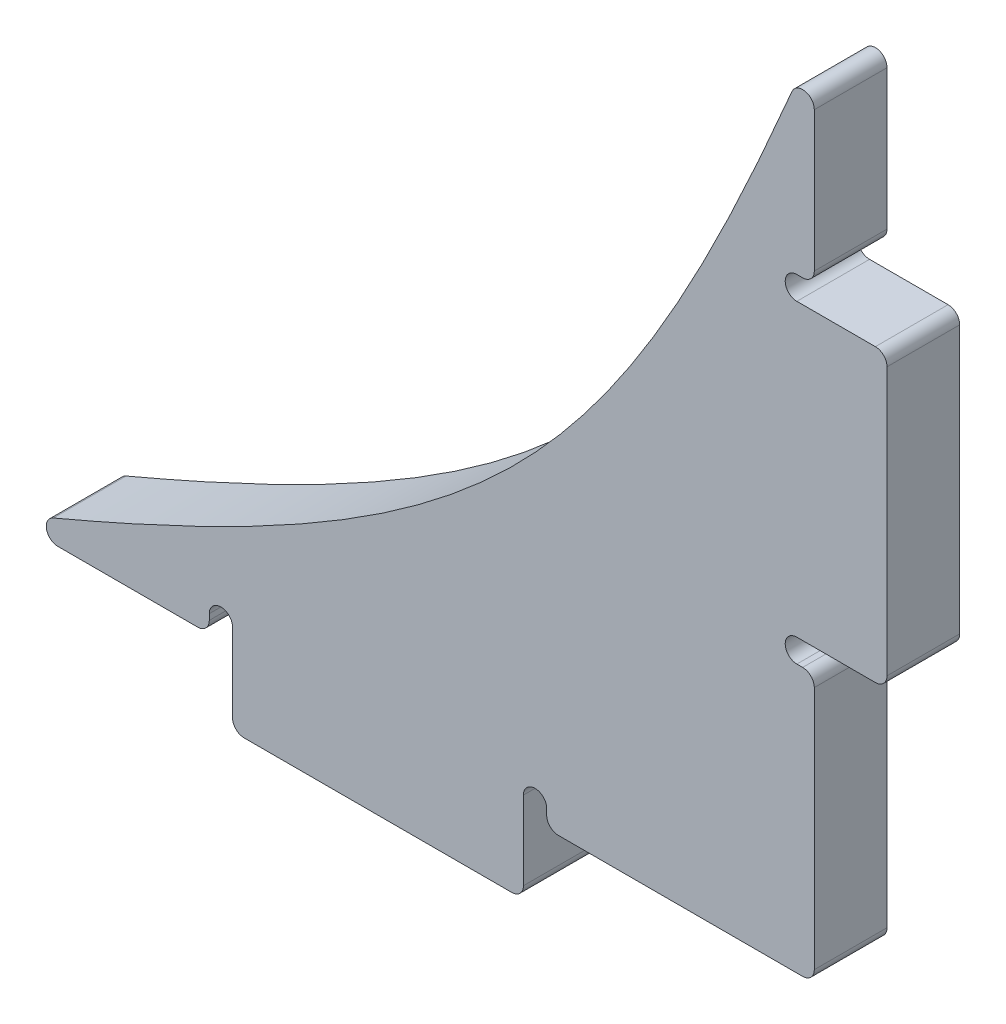
SolidWorks part; units mm, degrees
material "6061-T6 (SS)"
ref_plane "Front Plane" through (0, 0, 0) normal (0, 0, 1) x (1, 0, 0)
ref_plane "Top Plane" through (0, 0, 0) normal (0, 1, 0) x (1, 0, 0)
ref_plane "Right Plane" through (0, 0, 0) normal (1, 0, 0) x (0, 0, -1)
sketch "Sketch1" plane through (0, 0, 0) normal (0, 0, 1) x (1, 0, 0)
  line L0 (22.86, 22.86) -> (14.0603, 1.4879) construction
  line L1 (22.86, -12.7) -> (-12.7, -12.7)
  line L2 (22.86, -12.7) -> (22.86, 22.86)
  line L5 (5.08, 5.08) -> (22.86, -12.7) construction
  line L6 (22.86, 22.86) -> (-12.7, -12.7) construction
  line L7 (14.0603, 1.4879) -> (8.6721, -3.9003) construction
  line L8 (8.6721, -3.9003) -> (-12.7, -12.7) construction
  spline S0 degree 3 poles (22.86, 22.86) (14.0603, 1.4879) (8.6721, -3.9003) (-12.7, -12.7) knots 0 0 0 0 1 1 1 1
  point P0 (0, 0)
  point P9 (11.3662, -1.2062)
  dimension "D1" = 35.56
  dimension "D2" = 35.56
  dimension "D3" = 7.62
  dimension "D4" = 12.7
  dimension "D5" = 17.78
extrude "Boss-Extrude1" add sketch "Sketch1" along normal blind 3.175
sketch "Sketch2" plane through (0, -12.7, 0) normal (0, -1, 0) x (1, 0, 0)
  line L0 (-12.7, 3.175) -> (22.86, 3.175) construction
  line L1 (-2.54, 3.175) -> (10.16, 3.175)
  line L2 (-2.54, 3.175) -> (-2.54, 0)
  line L3 (-2.54, 0) -> (10.16, 0)
  line L4 (10.16, 3.175) -> (10.16, 0)
  line L5 (-12.7, 0) -> (22.86, 0) construction
  line L6 (22.86, 3.175) -> (22.86, 0) construction
  dimension "D1" = 12.7
  dimension "D2" = 12.7
extrude "Boss-Extrude2" add sketch "Sketch2" along normal blind 3.175
sketch "Sketch3" plane through (22.86, 0, 0) normal (1, 0, 0) x (0, 0, -1)
  line L0 (-3.175, -12.7) -> (-3.175, 22.86) construction
  line L1 (-3.175, 0) -> (0, 0)
  line L2 (-3.175, 0) -> (-3.175, 12.7)
  line L3 (-3.175, 12.7) -> (0, 12.7)
  line L4 (0, 0) -> (0, 12.7)
  line L5 (0, -12.7) -> (0, 22.86) construction
  line L6 (-3.175, -12.7) -> (0, -12.7) construction
  dimension "D1" = 12.7
  dimension "D2" = 12.7
extrude "Boss-Extrude3" add sketch "Sketch3" along normal blind 3.175
sketch "Sketch4" plane through (0, 0, 3.175) normal (0, 0, 1) x (1, 0, 0)
  line L0 (-12.7, -12.7) -> (-2.54, -12.7) construction
  line L1 (10.16, -12.7) -> (22.86, -12.7) construction
  line L2 (22.86, -12.7) -> (22.86, 0) construction
  line L3 (22.86, 12.7) -> (22.86, 22.86) construction
  line L4 (-2.54, -15.875) -> (-2.54, -12.7) construction
  line L5 (10.16, -15.875) -> (10.16, -12.7) construction
  line L6 (26.035, 0) -> (22.86, 0) construction
  line L7 (26.035, 12.7) -> (22.86, 12.7) construction
  line L8 (-3.556, -11.938) -> (-3.556, -12.7)
  line L9 (-3.556, -12.7) -> (-2.54, -12.7)
  line L10 (-2.54, -12.7) -> (-2.54, -11.938)
  line L11 (10.16, -11.938) -> (10.16, -12.7)
  line L12 (10.16, -12.7) -> (11.176, -12.7)
  line L13 (11.176, -12.7) -> (11.176, -11.938)
  line L14 (22.098, -1.016) -> (22.86, -1.016)
  line L15 (22.86, -1.016) -> (22.86, 0)
  line L16 (22.86, 0) -> (22.098, 0)
  line L17 (22.098, 12.7) -> (22.86, 12.7)
  line L18 (22.86, 12.7) -> (22.86, 13.716)
  line L19 (22.86, 13.716) -> (22.098, 13.716)
  arc A0 (-2.54, -11.938) -> (-3.556, -11.938) centre (-3.048, -11.938) ccw
  arc A1 (11.176, -11.938) -> (10.16, -11.938) centre (10.668, -11.938) ccw
  arc A2 (22.098, 0) -> (22.098, -1.016) centre (22.098, -0.508) ccw
  arc A3 (22.098, 13.716) -> (22.098, 12.7) centre (22.098, 13.208) ccw
  dimension "D1" = 1.016
  dimension "D2" = 1.016
  dimension "D3" = 1.016
  dimension "D4" = 1.016
  dimension "D5" = 0.762
  dimension "D6" = 0.762
  dimension "D7" = 0.762
  dimension "D8" = 0.762
extrude "Cut-Extrude1" cut sketch "Sketch4" against normal up to next
fillet "Fillet1" radius 0.508 11 edges at (22.86, 13.716, 1.5875) (26.035, 12.7, 1.5875) (26.035, 0, 1.5875) (22.86, -1.016, 1.5875) (22.86, -12.7, 1.5875) (11.176, -12.7, 1.5875) (10.16, -15.875, 1.5875) (-2.54, -15.875, 1.5875) (-3.556, -12.7, 1.5875) (-12.7, -12.7, 1.5875) (22.86, 22.86, 1.5875)
scale "Scale1" scale about centroid uniform scaling yes scale factor 0.35
